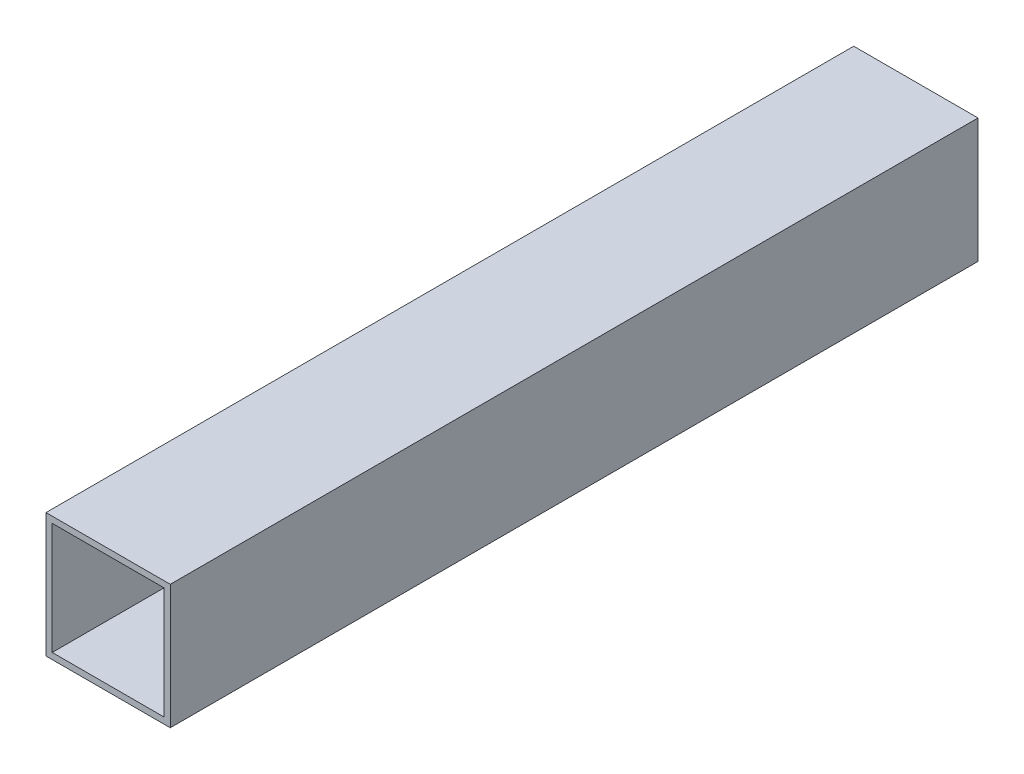
SolidWorks part; units mm, degrees
material "Plain Carbon Steel"
ref_plane "Front Plane" through (0, 0, 0) normal (0, 0, 1) x (1, 0, 0)
ref_plane "Top Plane" through (0, 0, 0) normal (0, 1, 0) x (1, 0, 0)
ref_plane "Right Plane" through (0, 0, 0) normal (1, 0, 0) x (0, 0, -1)
sketch "Sketch1" plane through (0, 0, 0) normal (0, 0, 1) x (1, 0, 0)
  line B0 (-50, -50) -> (50, -50)
  line B1 (-50, -50) -> (-50, 50)
  line B2 (50, -50) -> (50, 50)
  line B3 (-50, 50) -> (50, 50)
  line B4 (-45, -45) -> (45, -45)
  line B5 (-45, -45) -> (-45, 45)
  line B6 (45, -45) -> (45, 45)
  line B7 (-45, 45) -> (45, 45)
sketch_block_instance "10x10x5_profil-1"
sketch_block "10x10x5_profil" parameters "D1"=100, "D2"=100, "D3"=5, "D4"=5
extrude "Boss-Extrude1" add sketch "Sketch1" along normal mid plane 650
